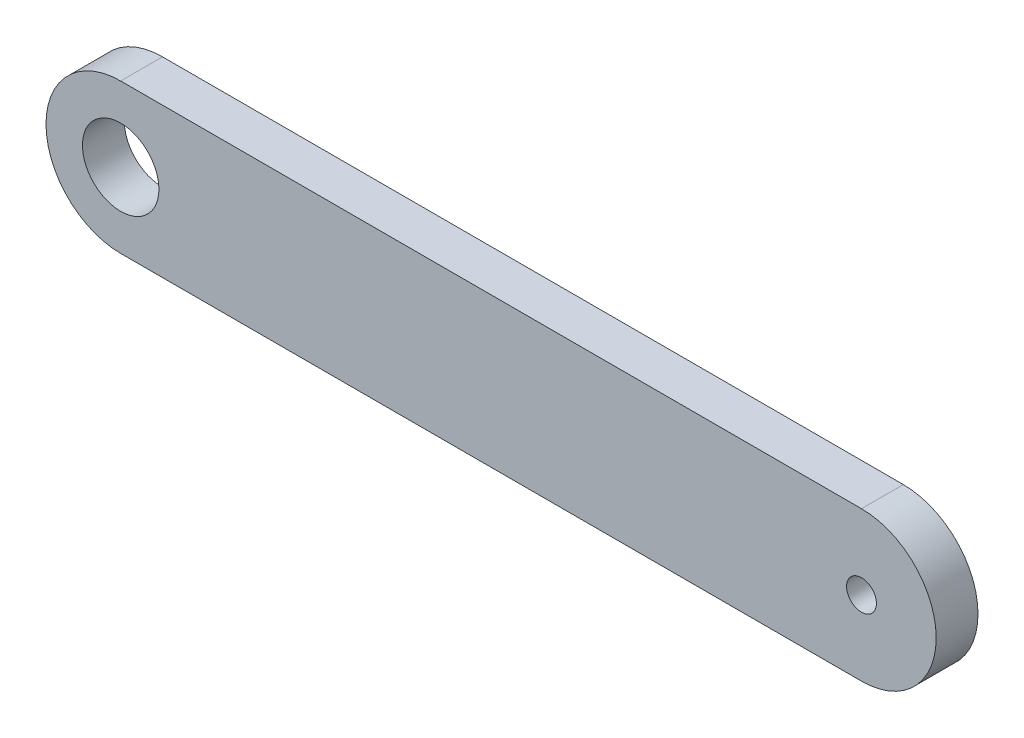
SolidWorks part; units mm, degrees
ref_plane "Front Plane" through (0, 0, 0) normal (0, 0, 1) x (1, 0, 0)
ref_plane "Top Plane" through (0, 0, 0) normal (0, 1, 0) x (1, 0, 0)
ref_plane "Right Plane" through (0, 0, 0) normal (1, 0, 0) x (0, 0, -1)
sketch "Sketch1" plane through (0, 0, 0) normal (0, 0, 1) x (1, 0, 0)
  line L0 (0, 0) -> (31, 0) construction
  line L1 (0, 3.125) -> (31, 3.125)
  line L2 (0, -3.125) -> (31, -3.125)
  arc A0 (0, 3.125) -> (0, -3.125) centre (0, 0) ccw
  arc A1 (31, -3.125) -> (31, 3.125) centre (31, 0) ccw
  circle A2 centre (0, 0) radius 1.6
  circle A3 centre (31, 0) radius 0.625
  point P3 (15.5, 0)
  dimension "D2" = 3.2
  dimension "D3" = 3.125
  dimension "D4" = 1.25
  dimension "D1" = 31
extrude "Boss-Extrude1" add sketch "Sketch1" along normal blind 1.75 contours L1 A1 L2 A0
